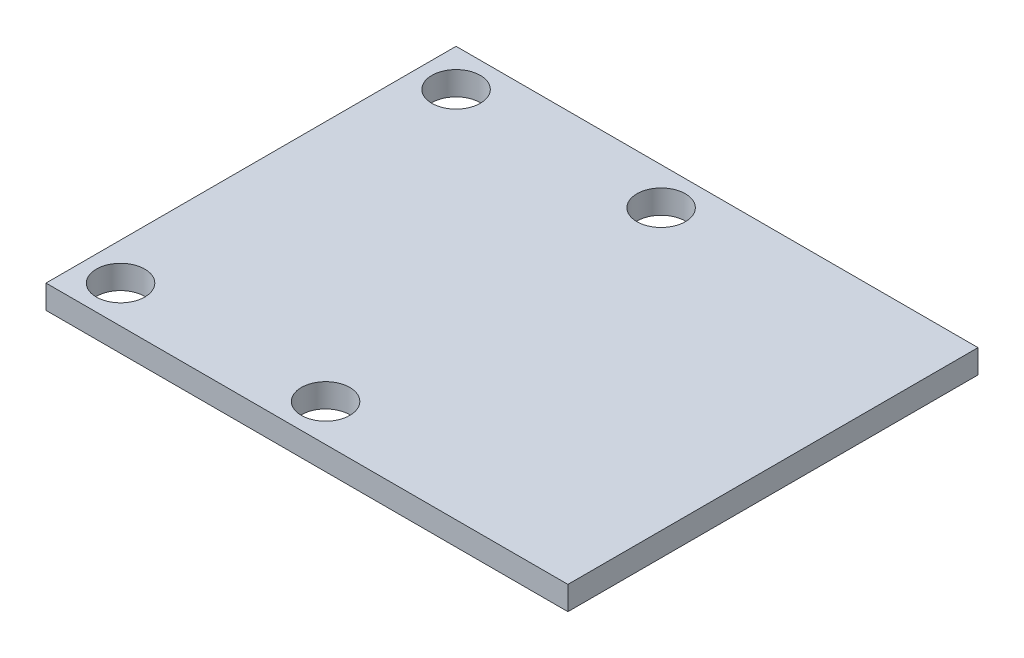
SolidWorks part; units mm, degrees
material "Copper"
ref_plane "Front Plane" through (0, 0, 0) normal (0, 0, 1) x (1, 0, 0)
ref_plane "Top Plane" through (0, 0, 0) normal (0, 1, 0) x (1, 0, 0)
ref_plane "Right Plane" through (0, 0, 0) normal (1, 0, 0) x (0, 0, -1)
sketch "Sketch1" plane through (0, 0, 0) normal (0, 1, 0) x (1, 0, 0)
  line L0 (14, 11) -> (-14, -11) construction
  line L1 (-14, 11) -> (14, 11)
  line L2 (-14, 11) -> (-14, -11)
  line L3 (-14, -11) -> (14, -11)
  line L4 (14, 11) -> (14, -11)
  point P4 (0, 0)
  dimension "D1" = 28
  dimension "D2" = 22
extrude "Boss-Extrude1" add sketch "Sketch1" along normal blind 1.27
sketch "Sketch2" plane through (0, 0, 0) normal (0, 1, 0) x (1, 0, 0)
  line L1 (14, 11) -> (-14, 11) construction
  line L2 (-14, 11) -> (-14, -11) construction
  circle A0 centre (-12, 9) radius 1.3
  dimension "D1" = 2.6
  dimension "D2" = 2
  dimension "D3" = 2
extrude "Cut-Extrude2" cut sketch "Sketch2" along normal through all
pattern_linear "LPattern1" count 2 spacing 11 along (1, 0, 0) count 2 spacing 18 along (0, 0, 1) of "Cut-Extrude2"
